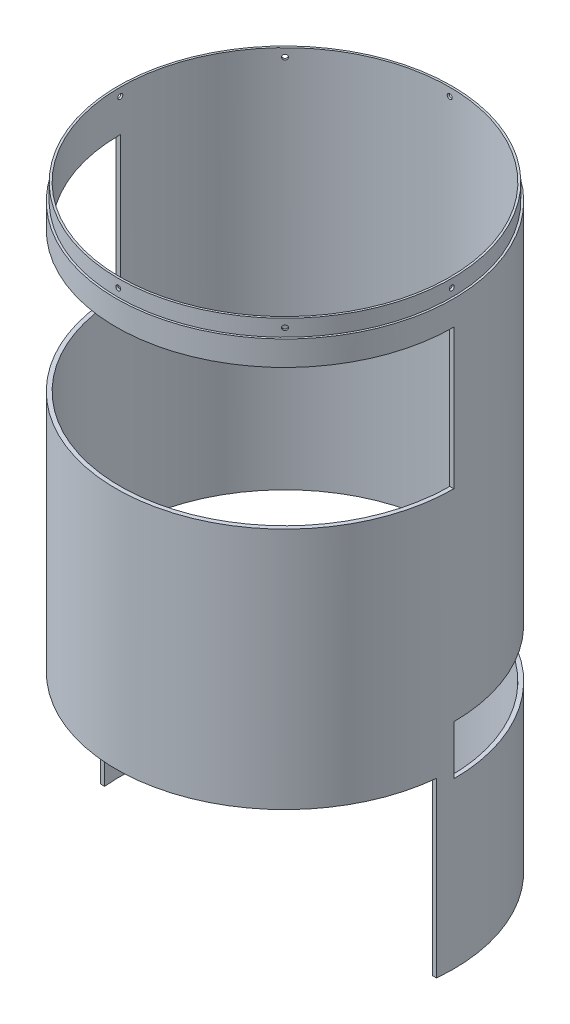
SolidWorks part; units mm, degrees
material "PLA"
ref_plane "Front Plane" through (0, 0, 0) normal (0, 0, 1) x (1, 0, 0)
ref_plane "Top Plane" through (0, 0, 0) normal (0, 1, 0) x (1, 0, 0)
ref_plane "Right Plane" through (0, 0, 0) normal (1, 0, 0) x (0, 0, -1)
sketch "Sketch1" plane through (0, 0, 0) normal (0, 1, 0) x (1, 0, 0)
  circle A0 centre (0, 0) radius 205
  dimension "D1" = 410
extrude "Boss-Extrude1" add sketch "Sketch1" along normal blind 705
sketch "Sketch17" plane through (0, 0, 0) normal (0, 1, 0) x (1, 0, 0)
  line L0 (-204.0221, -20) -> (204.0221, -20)
  arc A0 (-204.0221, -20) -> (204.0221, -20) centre (0, 0) ccw
  dimension "D1" = 410
  dimension "D2" = 20
extrude "Cut-Extrude14" cut sketch "Sketch17" along normal blind 210
shell "Shell1" thickness 5
ref_plane "Plane3" through (0, 675, 0) normal (0, 1, 0) x (1, 0, 0)
sketch "Sketch18" plane through (0, 675, 0) normal (0, 1, 0) x (1, 0, 0)
  line L0 (-205, 0) -> (205, 0)
  circle A0 centre (0, 0) radius 205 construction
  arc A1 (-205, 0) -> (205, 0) centre (0, 0) ccw
extrude "Cut-Extrude15" cut sketch "Sketch18" against normal blind 170
ref_plane "Plane4" through (0, 260, 0) normal (0, -1, 0) x (-1, 0, 0)
sketch "Sketch19" plane through (0, 260, 0) normal (0, -1, 0) x (-1, 0, 0)
  line L0 (-205, 0) -> (205, 0)
  arc A0 (205, 0) -> (-205, 0) centre (0, 0) ccw
  dimension "D1" = 410
extrude "Cut-Extrude16" cut sketch "Sketch19" along normal blind 60
sketch "Sketch22" plane through (0, 705, 0) normal (0, 1, 0) x (1, 0, 0)
  circle A0 centre (0, 0) radius 200 construction
  circle A1 centre (0, 0) radius 200
  circle A2 centre (0, 0) radius 202.5
  dimension "D1" = 2.5
extrude "Boss-Extrude4" add sketch "Sketch22" along normal blind 20
sketch "Sketch26" plane through (0, 0, 0) normal (0, 0, 1) x (1, 0, 0)
  line L0 (0, 734.5332) -> (0, 0) construction
  line L1 (202.5, 725) -> (-202.5, 725) construction
  circle A0 centre (0, 715) radius 3
  dimension "D1" = 6
  dimension "D2" = 10
extrude "Cut-Extrude18" cut sketch "Sketch26" against normal through all both and the other way through all
sketch "Sketch28" plane through (0, 0, 0) normal (0, 0, 1) x (1, 0, 0)
  line L0 (0, 832.5379) -> (0, -67.4621) construction
  dimension "D1" = 900
pattern_circular "CirPattern1" count 4 every 45 about axis through (0, 832.5379, 0) along (0, -1, 0) of "Cut-Extrude18"
